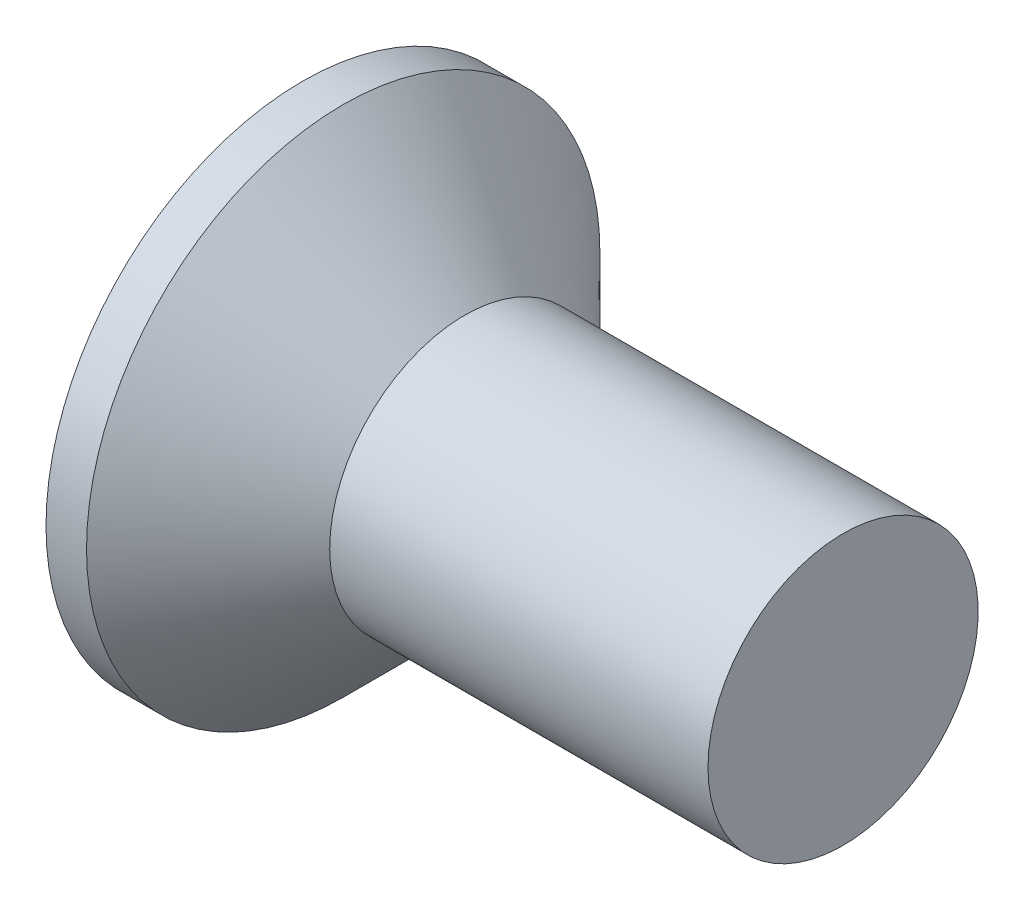
SolidWorks part; units mm, degrees
ref_plane "Plane1" through (0, 0, 0) normal (0, 0, 1) x (1, 0, 0)
ref_plane "Plane2" through (0, 0, 0) normal (0, 1, 0) x (1, 0, 0)
ref_plane "Plane3" through (0, 0, 0) normal (1, 0, 0) x (0, 0, -1)
sketch "BodySke" plane through (0, 0, 0) normal (0, 0, 1) x (1, 0, 0)
  line L0 (0, 0) -> (0, 1.9)
  line L1 (0, 1.9) -> (0.3, 1.9)
  line L2 (1.2, 1) -> (4, 1)
  line L3 (4, 1) -> (4, 0)
  line L4 (4, 0) -> (0, 0)
  line L5 (-6.35, 0) -> (82.55, 0) construction
  line L6 (1.2, -1) -> (4, -1) construction
  line L7 (0.3, -1.9) -> (1.2, -1) construction
  line L8 (0.3, 1.9) -> (1.2, 1)
  line L9 (0, -1.9) -> (0.3, -1.9) construction
  line L10 (1.6, 2.5875) -> (1.6, -6.9375) construction
  line L11 (1, 6.35) -> (1, -3.175) construction
  dimension "Diameter" = 2
  dimension "Length" = 4
  dimension "Head_ht" = 1.2
  dimension "Head_dia" = 3.8
  dimension "Head_ang" = 90
  dimension "D6" = 0.3
  dimension "Advance" = 0.4
  dimension "Thread_nom" = 3
revolve "Base-Revolve" add sketch "BodySke" angle 360 about L5
cosmetic thread "ThreadCosmetic" [suppressed] parameters "Thread_length"=2.4, "Thread_minor"=1.548
sketch "Sketch2" plane through (0, 0, 0) normal (-1, 0, 0) x (0, 0, 1)
  line L0 (-1.9, -0.35) -> (1.9, -0.35)
  line L1 (-1.9, -0.35) -> (-1.9, 0.35)
  line L2 (1.9, 0.35) -> (-1.9, 0.35)
  line L3 (1.9, 0.35) -> (1.9, -0.35)
  dimension "D1" = 0.35
  dimension "Slot_width" = 0.7
  dimension "D2" = 3.8
  dimension "D3" = 1.9
extrude "Slot" [suppressed] cut sketch "Sketch2" against normal blind 0.6
sketch "Sketch3" plane through (0, 0, 0) normal (-1, 0, 0) x (0, 0, 1)
  line L0 (-0.265, 1.07) -> (0.265, 1.07)
  line L1 (0.265, 1.07) -> (0.265, -1.07)
  line L2 (0.265, -1.07) -> (-0.265, -1.07)
  line L3 (-0.265, -1.07) -> (-0.265, 1.07)
  dimension "D1" = 1.07
  dimension "Cross_dia" = 2.14
  dimension "D2" = 0.265
  dimension "Cross_width" = 0.53
ref_plane "Plane4" through (1.54, 0, 0) normal (-1, 0, 0) x (0, 0, 1)
sketch "Sketch4" plane through (1.54, 0, 0) normal (-1, 0, 0) x (0, 0, 1)
  line L0 (-0.1325, 0.1325) -> (0.1325, 0.1325)
  line L3 (0.1325, 0.1325) -> (0.1325, -0.1325)
  line L4 (0.1325, -0.1325) -> (-0.1325, -0.1325)
  line L5 (-0.1325, -0.1325) -> (-0.1325, 0.1325)
  dimension "D1" = 0.265
  dimension "D2" = 0.265
  dimension "D3" = 0.1325
  dimension "D4" = 0.1325
loft "Cross" cut profiles "Sketch3", "Sketch4"
pattern_circular "CirPattern1" count 2 every 90 about axis through (0, 0, 0) along (1, 0, 0) of "Cross"
sketch "ThdSchSke" plane through (0, 0, 0) normal (0, 0, 1) x (1, 0, 0)
  line L0 (1.6, -0.774) -> (1.4418, -1)
  line L1 (1.6, -0.774) -> (1.7582, -1)
  line L2 (1.7582, -1) -> (1.7582, -1.25)
  line L3 (-3.175, 0) -> (5.1513, 0) construction
  line L5 (1.7582, -1.25) -> (1.4418, -1.25)
  line L6 (1.4418, -1.25) -> (1.4418, -1)
  line L7 (0, 1.9) -> (0, -1.9) construction
  dimension "Thread_minor" = 1.548
  dimension "Diameter" = 2
  dimension "Start" = 1.6
  dimension "SideAngle" = 55
  dimension "VeeAngle" = 70
  dimension "Overcut" = 2.5
revolve "ThreadSchematic" [suppressed] cut sketch "ThdSchSke" angle 360 about L3
pattern_linear "ThdSchPat" [suppressed]
equation "\"D1@Sketch3\" = \"Cross_dia@Sketch3\" / 2"
equation "\"D2@Sketch3\" = \"Cross_width@Sketch3\" / 2"
equation "\"D1@Sketch4\" = \"Cross_width@Sketch3\" *.5"
equation "\"D2@Sketch4\" = \"D1@Sketch4\""
equation "\"D4@Sketch4\" = \"D2@Sketch4\" / 2"
equation "\"D3@Sketch4\" = \"D1@Sketch4\" / 2"
equation "\"D1@Sketch2\" = \"Slot_width@Sketch2\" / 2"
equation "\"D2@Sketch2\" = \"Head_dia@BodySke\""
equation "\"D3@Sketch2\" = \"D2@Sketch2\" / 2"
equation "\"Thread_length@ThreadCosmetic\" = ((sgn( (\"Length@BodySke\" - \"Advance@BodySke\" - \"Head_ht@BodySke\" ) - \"Thread_nom@BodySke\" )-1)*( (\"Length@BodySke\" - \"Advance@BodySke\" - \"Head_ht@BodySke\" ) - \"Thread_nom@BodySke\" ))/-2+ \"Thread_nom@BodySke\""
equation "\"Thread_minor@ThdSchSke\" = \"Thread_minor@ThreadCosmetic\""
equation "\"Diameter@ThdSchSke\" = \"Diameter@BodySke\""
equation "\"Overcut@ThdSchSke\" = \"Diameter@BodySke\" * 1.25"
equation "\"Start@ThdSchSke\" = 0.000001 + \"Length@BodySke\" - \"Thread_length@ThreadCosmetic\"  '---Countersunk---"
equation "\"Num_threads@ThdSchPat\" = int( \"Thread_length@ThreadCosmetic\" / \"Advance@BodySke\" + 0.999 )  + 1"
equation "\"Advance@ThdSchPat\" = \"Thread_length@ThreadCosmetic\" /  (\"Num_threads@ThdSchPat\" - 1) 'relax it"
